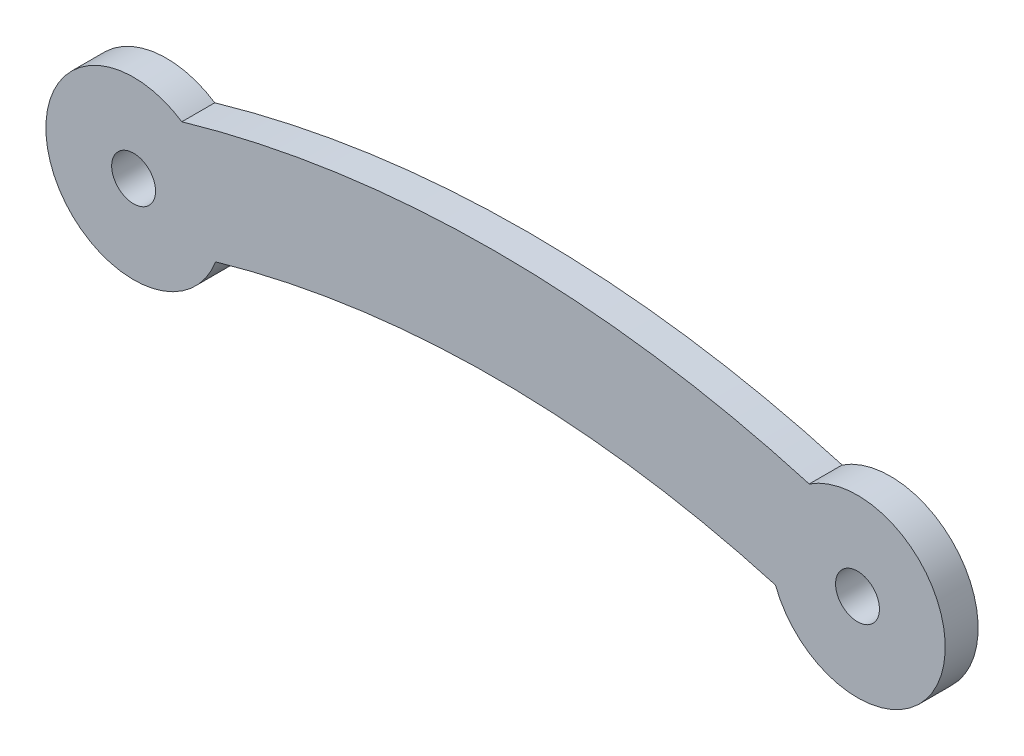
SolidWorks part; units mm, degrees
material "Galvanized Steel"
ref_plane "Front Plane" through (0, 0, 0) normal (0, 0, 1) x (1, 0, 0)
ref_plane "Top Plane" through (0, 0, 0) normal (0, 1, 0) x (1, 0, 0)
ref_plane "Right Plane" through (0, 0, 0) normal (1, 0, 0) x (0, 0, -1)
sketch "Sketch1" plane through (0, 0, 0) normal (0, 0, 1) x (1, 0, 0)
  line L0 (0, 0) -> (2.5, 0) construction
  line L1 (16.5, 0) -> (16.5, 5.3742) construction
  line L2 (0, -4) -> (33, -4) construction
  line L3 (4, 0) -> (29, 0) construction
  line L4 (30.5, 0) -> (33, 0) construction
  circle A0 centre (0, 0) radius 1
  circle A1 centre (33, 0) radius 1
  arc A2 (2.1999, 3.3407) -> (3.7399, -1.4189) centre (0, 0) ccw
  arc A3 (29.2601, -1.4189) -> (30.8001, 3.3407) centre (33, 0) ccw
  circle A4 centre (0, 0) radius 2.5 construction
  circle A5 centre (33, 0) radius 2.5 construction
  arc A6 (2.1999, 3.3407) -> (30.8001, 3.3407) centre (16.5, -45.9245) cw
  arc A7 (3.7399, -1.4189) -> (29.2601, -1.4189) centre (16.5, -45.9245) cw
  arc A8 (0.8453, -2.3528) -> (32.1547, -2.3528) centre (16.5, -45.9245) cw construction
  arc A9 (-0.8453, 2.3528) -> (33.8453, 2.3528) centre (16.5, -45.9245) cw construction
  point P16 (0, 0)
  dimension "D2" = 2
  dimension "D3" = 2
  dimension "D4" = 8
  dimension "D5" = 8
  dimension "D6" = 5
  dimension "D7" = 5
  dimension "D9" = 51.2987
  dimension "D1" = 33
  dimension "D8" = 5
extrude "Boss-Extrude1" add sketch "Sketch1" along normal blind 1.5
